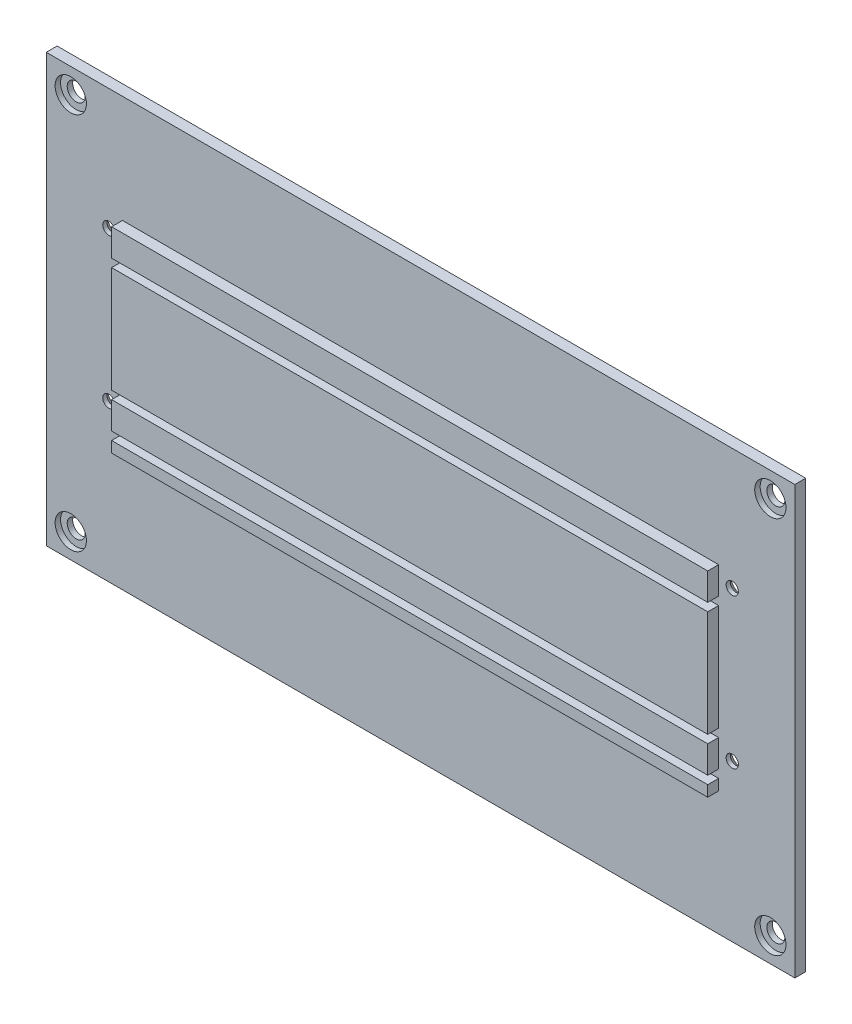
SolidWorks part; units mm, degrees
ref_plane "Plan de face" through (0, 0, 0) normal (0, 0, 1) x (1, 0, 0)
ref_plane "Plan de dessus" through (0, 0, 0) normal (0, 1, 0) x (1, 0, 0)
ref_plane "Plan de droite" through (0, 0, 0) normal (1, 0, 0) x (0, 0, -1)
sketch "Esquisse4" plane through (0, 0, 0) normal (0, 0, 1) x (1, 0, 0)
  line L0 (-137.5, 78.5) -> (-137.5, -78.5)
  line L1 (-137.5, -78.5) -> (137.5, -78.5)
  line L2 (0, -2.2) -> (0, 2.2) construction
  line L3 (137.5, 78.5) -> (137.5, -78.5)
  line L4 (2.2, 0) -> (-2.2, 0) construction
  line L5 (-137.5, 78.5) -> (137.5, 78.5)
  dimension "D1" = 157
  dimension "D2" = 275
extrude "Boss.-Extru.2" add sketch "Esquisse4" along normal blind 4
sketch "Esquisse5" plane through (0, 0, 0) normal (0, 0, -1) x (-1, 0, 0)
  line L0 (-114.5, 78.5) -> (-114.5, -78.5) construction
  line L1 (-137.5, 78.5) -> (137.5, 78.5) construction
  line L2 (137.5, -78.5) -> (-137.5, -78.5) construction
  line L3 (-137.5, -78.5) -> (-137.5, 78.5) construction
  line L4 (0, 2.2) -> (0, -2.2) construction
  point P8 (-114.5, 34)
  point P9 (-114.5, -21)
  point P12 (114.5, 34)
  point P13 (114.5, -21)
  dimension "D1" = 23
  dimension "D2" = 44.5
  dimension "D3" = 57.5
hole_wizard "Fraisage pour vis à tête fraisée M42" positions "Esquisse5" profile "Esquisse6" countersink size "M4" standard "Ansi Metric" end condition through all
sketch "Esquisse6" plane through (-114.5, -21, 0) normal (1, 0, 0) x (0, 1, 0)
  line L0 (0, 0) -> (0, 4)
  line L1 (0, 4) -> (2.25, 4)
  line L2 (2.25, 4) -> (2.25, 2.45)
  line L3 (2.25, 2.45) -> (4.7, 0)
  line L5 (4.7, 0) -> (0, 0)
  line L6 (-2.25, 2.45) -> (-4.7, 0) construction
  line L11 (0, -6.35) -> (0, 107.95) construction
  dimension "Diamètre du perçage jusqu'au prochain" = 4.5
  dimension "Profondeur du perçage jusqu'au prochain" = 4
  dimension "Diamètre du fraisage entrant" = 9.4
  dimension "Angle du fraisage entrant" = 90
sketch "Esquisse7" plane through (0, 0, 4) normal (0, 0, 1) x (1, 0, 0)
  line L0 (-137.5, -69.5) -> (-128.5, -69.5) construction
  line L1 (-137.5, 78.5) -> (-137.5, -78.5) construction
  line L2 (-128.5, -69.5) -> (-128.5, -78.5) construction
  line L3 (-137.5, -78.5) -> (137.5, -78.5) construction
  line L4 (2.2, 0) -> (-2.2, 0) construction
  line L5 (0, -2.2) -> (0, 2.2) construction
  point P8 (-128.5, -69.5)
  point P10 (-128.5, 69.5)
  point P14 (128.5, 69.5)
  point P15 (128.5, -69.5)
  dimension "D1" = 9
  dimension "D2" = 9
hole_wizard "Chambrage pour Vis à tête ronde à 6 pans creux M61" positions "Esquisse7" profile "Esquisse8" counterbore size "M6" standard "Ansi Metric" end condition through all
sketch "Esquisse8" plane through (128.5, -69.5, 4) normal (1, 0, 0) x (0, -1, 0)
  line L0 (0, 0) -> (0, 4)
  line L1 (0, 4) -> (3.3, 4)
  line L3 (3.3, 4) -> (3.3, 2)
  line L4 (3.3, 2) -> (5.75, 2)
  line L5 (5.75, 2) -> (5.75, 0)
  line L7 (5.75, 0) -> (0, 0)
  line L11 (0, -6.35) -> (0, 107.95) construction
  dimension "Diamètre du perçage jusqu'au prochain" = 6.6
  dimension "Profondeur du perçage jusqu'au prochain" = 4
  dimension "Diamètre du chambrage" = 11.5
  dimension "Profondeur du chambrage" = 2
sketch "Esquisse9" plane through (0, 0, 4) normal (0, 0, 1) x (1, 0, 0)
  line L0 (114.5, -21) -> (115.5, -21) construction
  line L1 (115.5, -21) -> (115.5, -26) construction
  line L2 (115.5, -26) -> (115.5, -29)
  line L3 (115.5, -29) -> (109.5, -29)
  line L4 (109.5, -29) -> (109.5, -33)
  line L5 (115.5, -26) -> (109.5, -26)
  line L6 (109.5, -26) -> (109.5, -16)
  line L7 (109.5, -16) -> (115.5, -16)
  line L8 (115.5, -16) -> (115.5, -13)
  line L9 (115.5, -13) -> (109.5, -13)
  line L10 (109.5, -13) -> (109.5, 26)
  line L11 (109.5, 26) -> (115.5, 26)
  line L12 (115.5, 26) -> (115.5, 29)
  line L13 (115.5, 29) -> (109.5, 29)
  line L14 (109.5, 29) -> (109.5, 39)
  line L15 (109.5, 39) -> (-109.5, 39)
  line L16 (109.5, -33) -> (-109.5, -33)
  line L17 (0, -2.2) -> (0, 2.2) construction
  line L18 (-109.5, 29) -> (-109.5, 39)
  line L19 (-115.5, 29) -> (-109.5, 29)
  line L20 (-115.5, 26) -> (-115.5, 29)
  line L21 (-109.5, 26) -> (-115.5, 26)
  line L22 (-109.5, -13) -> (-109.5, 26)
  line L23 (-115.5, -13) -> (-109.5, -13)
  line L24 (-115.5, -16) -> (-115.5, -13)
  line L25 (-109.5, -16) -> (-115.5, -16)
  line L26 (-109.5, -26) -> (-109.5, -16)
  line L27 (-115.5, -26) -> (-109.5, -26)
  line L28 (-115.5, -26) -> (-115.5, -29)
  line L29 (-115.5, -29) -> (-109.5, -29)
  line L30 (-109.5, -29) -> (-109.5, -33)
  line L31 (-109.5, 29) -> (109.5, 29)
  line L32 (109.5, 26) -> (-109.5, 26)
  line L33 (109.5, -26) -> (-109.5, -26)
  line L34 (-109.5, -29) -> (109.5, -29)
  line L35 (-109.5, -13) -> (109.5, -13)
  line L36 (109.5, -16) -> (-109.5, -16)
  point P19 (0, 39)
  point P35 (0, -33)
  dimension "D1" = 1
  dimension "D2" = 5
  dimension "D3" = 3
  dimension "D4" = 6
  dimension "D5" = 4
  dimension "D6" = 10
  dimension "D7" = 39
extrude "Boss.-Extru.3" add sketch "Esquisse9" along normal blind 4 contours L18 L31 L14 L15 | L22 L35 L10 L32 | L6 L36 L26 L33 | L34 L30 L16 L4
